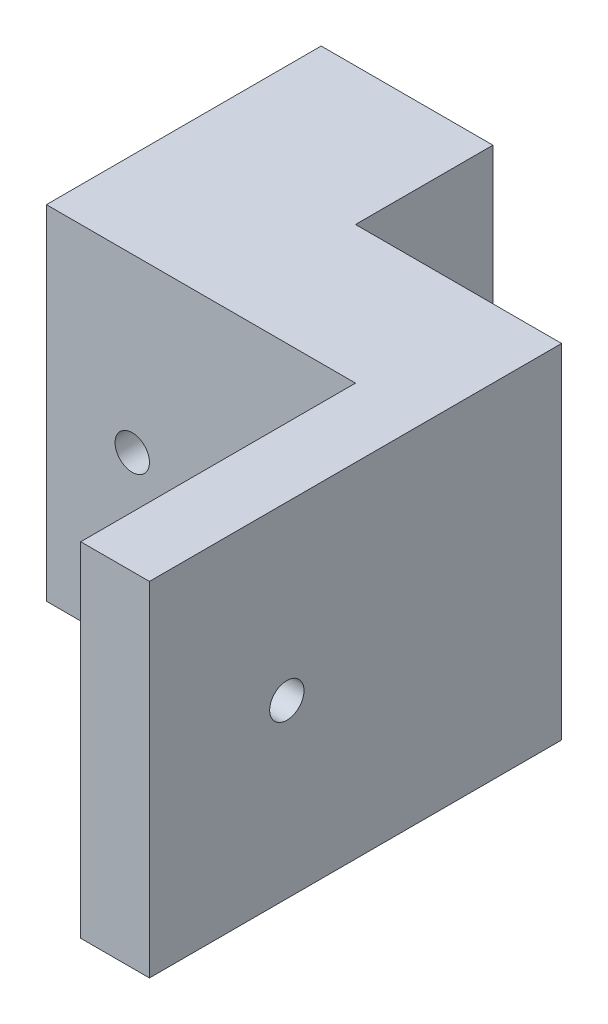
SolidWorks part; units mm, degrees
ref_plane "Alzado" through (0, 0, 0) normal (0, 0, 1) x (1, 0, 0)
ref_plane "Planta" through (0, 0, 0) normal (0, 1, 0) x (1, 0, 0)
ref_plane "Vista lateral" through (0, 0, 0) normal (1, 0, 0) x (0, 0, -1)
sketch "Croquis1" plane through (0, 0, 0) normal (0, 0, 1) x (1, 0, 0)
  line L0 (-41.0873, 30.3801) -> (-16.0873, 30.3801)
  line L1 (-16.0873, 30.3801) -> (-16.0873, -19.6199)
  line L2 (-41.0873, 30.3801) -> (-41.0873, -19.6199)
  line L3 (-41.0873, -19.6199) -> (-16.0873, -19.6199)
extrude "Saliente-Extruir1" add sketch "Croquis1" along normal blind 20
sketch "Croquis2" plane through (0, 0, 20) normal (0, 0, 1) x (1, 0, 0)
  line L0 (-41.0873, 30.3801) -> (3.9127, 30.3801)
  line L1 (-41.0873, -19.6199) -> (3.9127, -19.6199)
  line L2 (3.9127, -19.6199) -> (3.9127, 30.3801)
  line L3 (-41.0873, 30.3801) -> (-41.0873, -19.6199)
  dimension "D1" = 45
extrude "Saliente-Extruir2" add sketch "Croquis2" along normal blind 20
sketch "Croquis5" plane through (3.9127, 0, 0) normal (1, 0, 0) x (0, 0, -1)
  line L0 (-20, 30.3801) -> (-80, 30.3801)
  line L1 (-80, 30.3801) -> (-80, -19.6199)
  line L2 (-20, -19.6199) -> (-80, -19.6199)
  line L3 (-20, 30.3801) -> (-20, -19.6199)
  line L4 (-20, -19.6199) -> (-80, -19.6199)
  line L5 (-80, -19.6199) -> (-80, 30.3801)
  line L6 (-80, 30.3801) -> (-20, 30.3801)
  line M1 (-20, -19.6199) -> (-20, 30.3801)
  line M2 (-20, 30.3801) -> (-40, 30.3801)
  line M3 (-40, 30.3801) -> (-40, -19.6199)
  line M4 (-40, -19.6199) -> (-20, -19.6199)
  dimension "D1" = 60
extrude "Saliente-Extruir3" add sketch "Croquis5" along normal blind 10 contours M4 M1 M2 M3 | L2 L0 L1 M3
hole_wizard "Perforador para roscar para macho de roscar para M6x1.01" positions "Croquis3D2" profile "Croquis6" hole size "M6x1.0" standard "Ansi Metric"
sketch3d "Croquis3D2"
  line L0 (3.9127, 30.3801, 80) -> (3.9127, -19.6199, 80) construction
  line L1 (3.9127, -19.6199, 80) -> (3.9127, -19.6199, 40) construction
  line L2 (3.9127, -19.6199, 40) -> (3.9127, -19.6199, 80)
  point P0 (3.9127, 5.3801, 60)
  dimension "D1" = 20
  dimension "D2" = 25
sketch "Croquis6" plane through (3.9127, 5.3801, 60) normal (0, 1, 0) x (0, 0, 1)
  line L0 (0, 0) -> (0, 12.5022)
  line L1 (0, 12.5022) -> (2.5, 11)
  line L2 (2.5, 11) -> (2.5, 0)
  line L5 (2.5, 0) -> (0, 0)
  line L10 (0, 12.5022) -> (-2.5, 11) construction
  line L11 (0, -6.35) -> (0, 107.95) construction
  dimension "Diámetro de taladro" = 5
  dimension "Profundidad de taladro" = 11
  dimension "Ángulo de perforador" = 118
sketch "Croquis7" plane through (0, 30.3801, 0) normal (0, 1, 0) x (1, 0, 0)
  line L0 (13.9127, -80) -> (3.9127, -80)
  line L1 (3.9127, -80) -> (3.9127, -40)
  line L2 (3.9127, -40) -> (-41.0873, -40) construction
  line L3 (3.9127, -40) -> (3.9127, -80) construction
  point P4 (500000, -98.2758)
hole_wizard "Perforador para roscar para macho de roscar para M6x1.02" positions "Croquis3D3" profile "Croquis10" hole size "M6x1.0" standard "Ansi Metric" end condition through all
sketch3d "Croquis3D3"
  line L0 (-41.0873, 30.3801, 0) -> (-41.0873, -19.6199, 0) construction
  line L1 (-16.0873, 30.3801, 0) -> (-41.0873, 30.3801, 0) construction
  point P0 (-28.5873, 5.3801, 0)
  dimension "D1" = 12.5
  dimension "D2" = 25
sketch "Croquis10" plane through (-28.5873, 5.3801, 0) normal (1, 0, 0) x (0, 1, 0)
  line L0 (0, 0) -> (0, 80)
  line L1 (0, 80) -> (2.5, 80)
  line L2 (2.5, 80) -> (2.5, 0)
  line L5 (2.5, 0) -> (0, 0)
  line L11 (0, -6.35) -> (0, 107.95) construction
  dimension "Diámetro de taladro hasta el siguiente" = 5
  dimension "Profundidad de taladro hasta el siguiente" = 80
